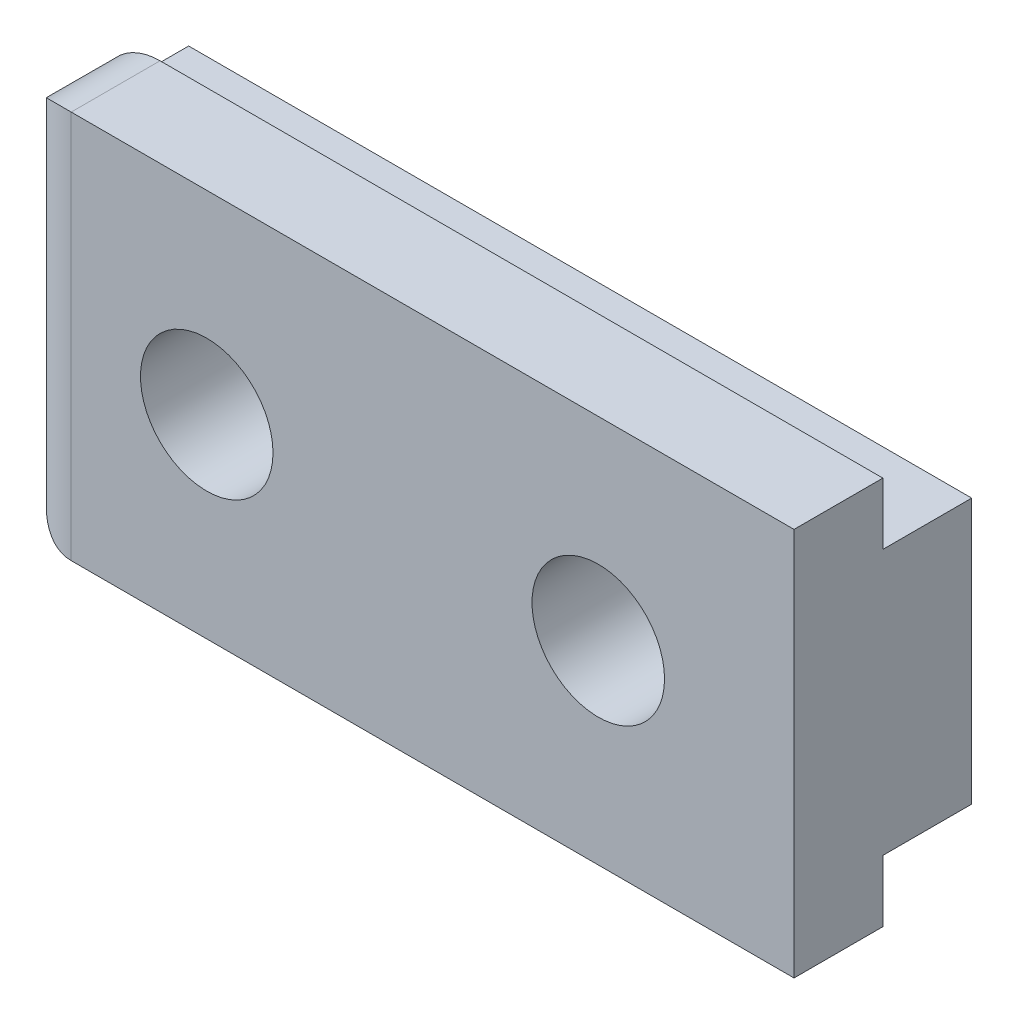
SolidWorks part; units mm, degrees
ref_plane "Front Plane" through (0, 0, 0) normal (0, 0, 1) x (1, 0, 0)
ref_plane "Top Plane" through (0, 0, 0) normal (0, 1, 0) x (1, 0, 0)
ref_plane "Right Plane" through (0, 0, 0) normal (1, 0, 0) x (0, 0, -1)
sketch "Sketch1" plane through (0, 0, 0) normal (0, 0, 1) x (1, 0, 0)
  line L1 (13, 6.45) -> (-13, 6.45)
  line L2 (13, 6.45) -> (13, -6.45)
  line L3 (13, -6.45) -> (-13, -6.45)
  line L4 (-13, 6.45) -> (-13, -6.45)
  line L5 (13, 6.45) -> (-13, -6.45) construction
  line L6 (13, -6.45) -> (-13, 6.45) construction
  point P0 (0, 0)
  dimension "D1" = 12.9
  dimension "D2" = 26
extrude "Boss-Extrude1" add sketch "Sketch1" along normal blind 5.9
sketch "Sketch2" plane through (13, 0, 0) normal (1, 0, 0) x (0, 0, -1)
  line L0 (-2.95, -6.45) -> (-2.95, 6.45) construction
  line L1 (-5.9, -6.45) -> (0, -6.45) construction
  line L2 (-5.9, 6.45) -> (0, 6.45) construction
  line L3 (0, 0) -> (-2.95, 0) construction
  line L4 (0, -6.45) -> (-2.95, -6.45)
  line L5 (0, -6.45) -> (0, -4.4)
  line L6 (0, -4.4) -> (-2.95, -4.4)
  line L7 (-2.95, -6.45) -> (-2.95, -4.4)
  line L8 (0, 4.4) -> (-2.95, 4.4)
  line L9 (-2.95, 6.45) -> (-2.95, 4.4)
  line L10 (0, 6.45) -> (-2.95, 6.45)
  line L11 (0, 6.45) -> (0, 4.4)
  line M6 (0, -6.45) -> (0, 6.45)
  line M7 (0, 6.45) -> (-5.9, 6.45)
  dimension "D1" = 2.05
extrude "Cut-Extrude1" cut sketch "Sketch2" against normal through all contours L9 L8 M7 M6 | L6 L7 L4 L5
hole_wizard "CSK SLOT for M2 Countersunk Flat Head Screw1" positions "Sketch4" profile "Sketch3" size "M2" standard "ISO" slot yes
sketch "Sketch4" plane through (0, 0, 5.9) normal (0, 0, 1) x (1, 0, 0)
  circle A0 centre (-6.5, 0) radius 0.625 construction
  circle A1 centre (6.5, 0) radius 0.625 construction
  point P1 (-6.5, 0)
  point P3 (6.5, 0)
sketch "Sketch3" plane through (-6.5, 0, 5.9) normal (1, 0, 0) x (0, -1, 0)
  line L0 (0, 0) -> (0, 6.621)
  line L1 (0, 6.621) -> (1.2, 5.9)
  line L2 (1.2, 5.9) -> (1.2, 5.5)
  line L3 (1.2, 5.5) -> (2.2, 4.5)
  line L4 (2.2, 4.5) -> (2.2, 0)
  line L6 (2.2, 0) -> (0, 0)
  line L7 (-1.2, 5.5) -> (-2.2, 4.5) construction
  line L10 (0, 6.621) -> (-1.2, 5.9) construction
  line L11 (0, -6.35) -> (0, 107.95) construction
  dimension "Hole Dia." = 2.4
  dimension "Hole Depth" = 5.9
  dimension "C'Sink Dia." = 4.4
  dimension "C'Sink Angle" = 90
  dimension "Drill Angle" = 118
  dimension "Head Clearance" = 4.5
fillet "Fillet1" radius 2 3 edges at (-13, 6.45, 4.425) (-13, 0, 5.9) (-13, -6.45, 4.425)
